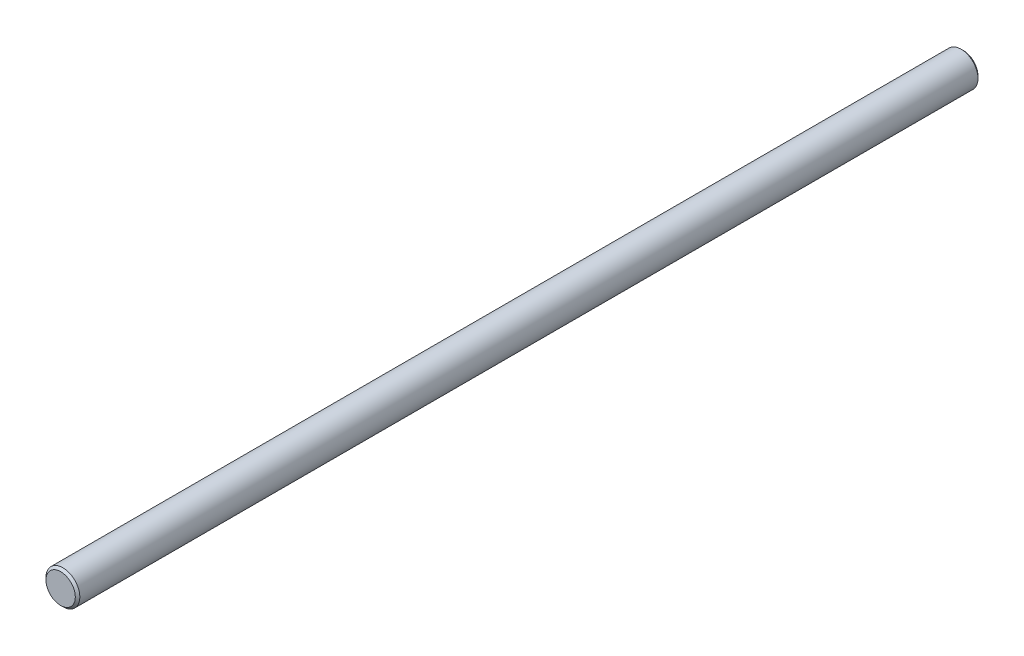
SolidWorks part; units mm, degrees
ref_plane "Front Plane" through (0, 0, 0) normal (0, 0, 1) x (1, 0, 0)
ref_plane "Top Plane" through (0, 0, 0) normal (0, 1, 0) x (1, 0, 0)
ref_plane "Right Plane" through (0, 0, 0) normal (1, 0, 0) x (0, 0, -1)
sketch "Sketch1" plane through (0, 0, 0) normal (0, 0, 1) x (1, 0, 0)
  circle A0 centre (0, 0) radius 4.7625
extrude "Boss-Extrude1" add sketch "Sketch1" along normal blind 254
chamfer "Chamfer1" distance 0.635 angle 45 2 edges at (4.7625, 0, 254) (4.7625, 0, 0)
